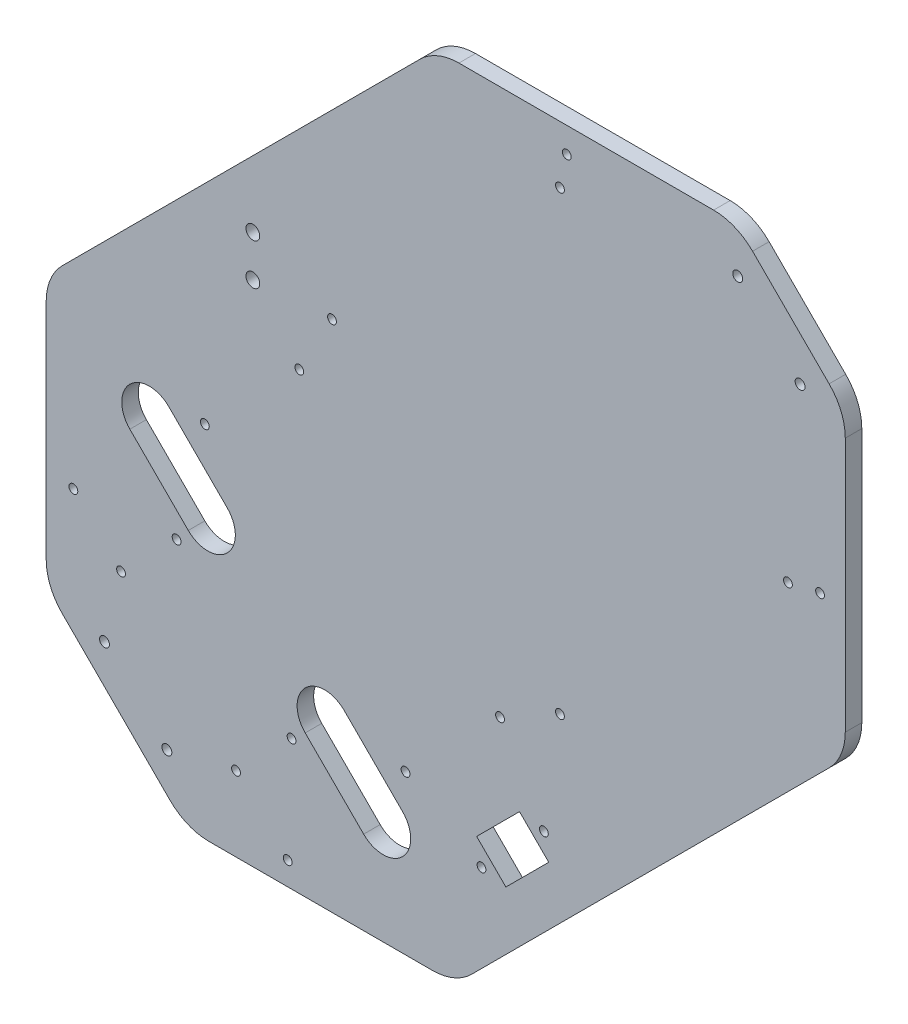
SolidWorks part; units mm, degrees
ref_plane "Front Plane" through (0, 0, 0) normal (0, 0, 1) x (1, 0, 0)
ref_plane "Top Plane" through (0, 0, 0) normal (0, 1, 0) x (1, 0, 0)
ref_plane "Right Plane" through (0, 0, 0) normal (1, 0, 0) x (0, 0, -1)
sketch "Sketch1" plane through (0, 0, 0) normal (0, 0, 1) x (1, 0, 0)
  line L0 (-157.3611, 14.7888) -> (-27.5692, 144.5806)
  line L1 (-168.2189, 155.4385) -> (131.7811, 155.4385) construction
  line L2 (-168.2189, 155.4385) -> (-168.2189, -144.5615) construction
  line L3 (-168.2189, -144.5615) -> (131.7811, -144.5615) construction
  line L4 (131.7811, 155.4385) -> (131.7811, -144.5615) construction
  line L5 (93.1414, 144.5806) -> (120.9232, 116.7989)
  line L6 (-157.3611, -94.6082) -> (-118.2656, -133.7036)
  line L7 (120.9232, -3.9118) -> (-8.8687, -133.7036)
  line L8 (131.7811, 155.4385) -> (-168.2189, -144.5615) construction
  line L9 (-142.056, -95.7711) -> (-119.4286, -118.3986) construction
  line L10 (87.7537, 134.0386) -> (110.3811, 111.4111) construction
  line L11 (-163.2189, 0.6466) -> (-163.2189, -80.4661)
  line L12 (-104.1235, -139.5615) -> (-23.0108, -139.5615)
  line L13 (126.7811, 10.2303) -> (126.7811, 102.6567)
  line L14 (-13.4271, 150.4385) -> (78.9993, 150.4385)
  line L15 (-153.3568, -53.3576) -> (-75.5751, -131.1393) construction
  line L16 (-59.4913, 46.8976) -> (23.2402, -35.8339) construction
  line L17 (-59.4913, 46.8976) -> (23.2402, 129.6291) construction
  line L18 (23.2402, -35.8339) -> (105.9717, 46.8976) construction
  line L19 (23.2402, 129.6291) -> (105.9717, 46.8976) construction
  line L20 (-71.3453, 25.1441) -> (1.4867, -47.6879) construction
  line L21 (-71.3453, 25.1441) -> (-105.64, -9.1506) construction
  line L22 (-105.64, -9.1506) -> (-32.808, -81.9826) construction
  line L23 (1.4867, -47.6879) -> (-32.808, -81.9826) construction
  line L24 (-115.893, -50.5163) -> (-74.1737, -92.2356) construction
  line L25 (-115.893, -50.5163) -> (-136.0456, -70.6688) construction
  line L26 (-136.0456, -70.6688) -> (-94.3263, -112.3881) construction
  line L27 (-74.1737, -92.2356) -> (-94.3263, -112.3881) construction
  line L28 (-125.7925, -17.2823) -> (-104.5793, -38.4955) construction
  line L29 (-118.7215, -10.2112) -> (-97.5083, -31.4244)
  line L30 (-132.8636, -24.3534) -> (-111.6504, -45.5666)
  line L31 (-62.1529, -80.9219) -> (-40.9397, -102.1351) construction
  line L32 (-55.0819, -73.8508) -> (-33.8687, -95.064)
  line L33 (-69.224, -87.993) -> (-48.0108, -109.2062)
  line L35 (-5.2308, -98.246) -> (17.3966, -75.6186) construction
  line L36 (25.715, 141.2964) -> (117.6389, 49.3725) construction
  line L37 (-88.2189, 59.8893) -> (-88.2189, 44.8893) construction
  line L38 (0.7796, -81.629) -> (11.3862, -92.2356) construction
  line L39 (-6.9986, -89.4072) -> (3.608, -100.0138)
  line L40 (-6.9986, -89.4072) -> (8.5577, -73.8508)
  line L41 (8.5577, -73.8508) -> (19.1644, -84.4574)
  line L42 (19.1644, -84.4574) -> (3.608, -100.0138)
  circle A0 centre (-142.056, -95.7711) radius 1.8
  circle A1 centre (-119.4286, -118.3986) radius 1.8
  circle A2 centre (87.7537, 134.0386) radius 1.8
  circle A3 centre (110.3811, 111.4111) radius 1.8
  arc A4 (-163.2189, 0.6466) -> (-157.3611, 14.7888) centre (-143.2189, 0.6466) cw
  arc A5 (-163.2189, -80.4661) -> (-157.3611, -94.6082) centre (-143.2189, -80.4661) ccw
  arc A6 (-104.1235, -139.5615) -> (-118.2656, -133.7036) centre (-104.1235, -119.5615) cw
  arc A7 (-23.0108, -139.5615) -> (-8.8687, -133.7036) centre (-23.0108, -119.5615) ccw
  arc A8 (126.7811, 10.2303) -> (120.9232, -3.9118) centre (106.7811, 10.2303) cw
  arc A9 (126.7811, 102.6567) -> (120.9232, 116.7989) centre (106.7811, 102.6567) ccw
  arc A10 (78.9993, 150.4385) -> (93.1414, 144.5806) centre (78.9993, 130.4385) cw
  arc A11 (-13.4271, 150.4385) -> (-27.5692, 144.5806) centre (-13.4271, 130.4385) ccw
  circle A12 centre (23.2402, 129.6291) radius 1.6
  circle A13 centre (-59.4913, 46.8976) radius 1.6
  circle A14 centre (105.9717, 46.8976) radius 1.6
  circle A15 centre (23.2402, -35.8339) radius 1.6
  circle A16 centre (-153.3568, -53.3576) radius 1.6
  circle A17 centre (-75.5751, -131.1393) radius 1.6
  circle A18 centre (-105.64, -9.1506) radius 1.6
  circle A19 centre (-32.808, -81.9826) radius 1.6
  circle A20 centre (1.4867, -47.6879) radius 1.6
  circle A21 centre (-71.3453, 25.1441) radius 1.6
  circle A22 centre (-136.0456, -70.6688) radius 1.6
  circle A23 centre (-94.3263, -112.3881) radius 1.6
  circle A24 centre (-74.1737, -92.2356) radius 1.6
  circle A25 centre (-115.893, -50.5163) radius 1.6
  arc A26 (-118.7215, -10.2112) -> (-132.8636, -24.3534) centre (-125.7925, -17.2823) ccw
  arc A27 (-111.6504, -45.5666) -> (-97.5083, -31.4244) centre (-104.5793, -38.4955) ccw
  arc A28 (-55.0819, -73.8508) -> (-69.224, -87.993) centre (-62.1529, -80.9219) ccw
  arc A29 (-48.0108, -109.2062) -> (-33.8687, -95.064) centre (-40.9397, -102.1351) ccw
  circle A32 centre (-5.2308, -98.246) radius 1.6
  circle A33 centre (17.3966, -75.6186) radius 1.6
  circle A34 centre (25.715, 141.2964) radius 1.6
  circle A35 centre (117.6389, 49.3725) radius 1.6
  circle A36 centre (-88.2189, 59.8893) radius 2.5
  circle A37 centre (-88.2189, 44.8893) radius 2.5
  point P6 (-69.224, -45.5666)
  point P8 (-130.7423, -107.0848)
  point P10 (99.0674, 122.7249)
  point P39 (-18.1256, 5.5319)
  point P61 (-115.1859, -91.5285)
  point P71 (-115.1859, -27.8889)
  point P76 (-51.5463, -91.5285)
  point P83 (0, 0)
  point P95 (71.677, 95.3344)
  point P102 (6.0829, -86.9323)
  point P103 (6.0829, -86.9323)
  point P106 (-1.6953, -94.7105)
  point P109 (0.7796, -81.629)
  dimension "D6" = 3.6
  dimension "D15" = 20
  dimension "D16" = 20
  dimension "D17" = 20
  dimension "D18" = 20
  dimension "D19" = 20
  dimension "D20" = 20
  dimension "D21" = 20
  dimension "D22" = 20
  dimension "D25" = 24
  dimension "D28" = 3.2
  dimension "D45" = 3.2
  dimension "D51" = 5
  dimension "D26" = 3.2
  dimension "D1" = 300
  dimension "D2" = 300
  dimension "D3" = 210
  dimension "D4" = 32
  dimension "D5" = 32
  dimension "D7" = 325
  dimension "D8" = 43
  dimension "D9" = 35
  dimension "D10" = 5
  dimension "D11" = 5
  dimension "D12" = 5
  dimension "D13" = 5
  dimension "D14" = 10
  dimension "D23" = 120
  dimension "D24" = 15
  dimension "D27" = 110
  dimension "D29" = 75
  dimension "D30" = 103
  dimension "D31" = 48.5
  dimension "D32" = 140
  dimension "D33" = 117
  dimension "D34" = 28.5
  dimension "D35" = 59
  dimension "D36" = 95
  dimension "D37" = 30
  dimension "D38" = 30
  dimension "D39" = 20
  dimension "D41" = 30
  dimension "D44" = 32
  dimension "D48" = 130
  dimension "D49" = 85
  dimension "D50" = 15
  dimension "D52" = 75
  dimension "D53" = 17
  dimension "D54" = 15
  dimension "D55" = 22
extrude "Boss-Extrude1" add sketch "Sketch1" along normal blind 6
